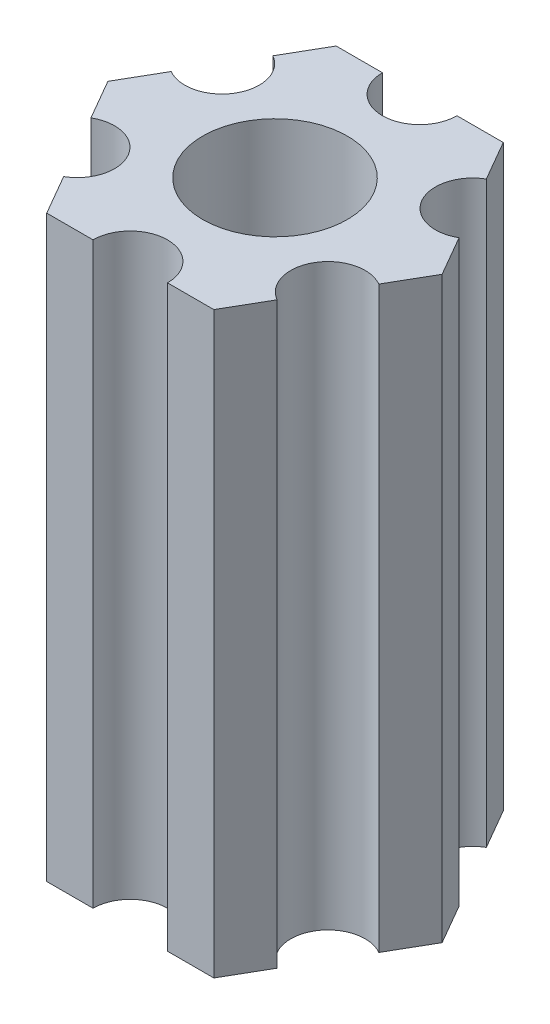
SolidWorks part; units mm, degrees
ref_plane "Front Plane" through (0, 0, 0) normal (0, 0, 1) x (1, 0, 0)
ref_plane "Top Plane" through (0, 0, 0) normal (0, 1, 0) x (1, 0, 0)
ref_plane "Right Plane" through (0, 0, 0) normal (1, 0, 0) x (0, 0, -1)
ref_plane "Plane1" through (0, -25.4, 0) normal (0, -1, 0) x (1, 0, 0)
sketch "Sketch1" plane through (0, -25.4, 0) normal (0, -1, 0) x (1, 0, 0)
  line L0 (-4.6822, -4.5902) -> (-3.6662, -6.35)
  line L1 (-3.6662, -6.35) -> (-1.6342, -6.35)
  line L2 (1.6342, -6.35) -> (3.6662, -6.35)
  line L3 (3.6662, -6.35) -> (4.6822, -4.5902)
  line L4 (6.3163, -1.7598) -> (7.3323, 0)
  line L5 (7.3323, 0) -> (6.3163, 1.7598)
  line L6 (4.6822, 4.5902) -> (3.6662, 6.35)
  line L7 (3.6662, 6.35) -> (1.6342, 6.35)
  line L8 (-1.6342, 6.35) -> (-3.6662, 6.35)
  line L9 (-3.6662, 6.35) -> (-4.6822, 4.5902)
  line L10 (-6.3163, 1.7598) -> (-7.3323, 0)
  line L11 (-7.3323, 0) -> (-6.3163, -1.7598)
  circle A0 centre (0, 0) radius 3.175
  arc A1 (-6.3163, -1.7598) -> (-4.6822, -4.5902) centre (-5.4993, -3.175) cw
  arc A2 (-1.6342, -6.35) -> (1.6342, -6.35) centre (0, -6.35) cw
  arc A3 (4.6822, -4.5902) -> (6.3163, -1.7598) centre (5.4993, -3.175) cw
  arc A4 (6.3163, 1.7598) -> (4.6822, 4.5902) centre (5.4993, 3.175) cw
  arc A5 (1.6342, 6.35) -> (-1.6342, 6.35) centre (0, 6.35) cw
  arc A6 (-4.6822, 4.5902) -> (-6.3163, 1.7598) centre (-5.4993, 3.175) cw
extrude "Boss-Extrude1" add sketch "Sketch1" against normal blind 25.4
